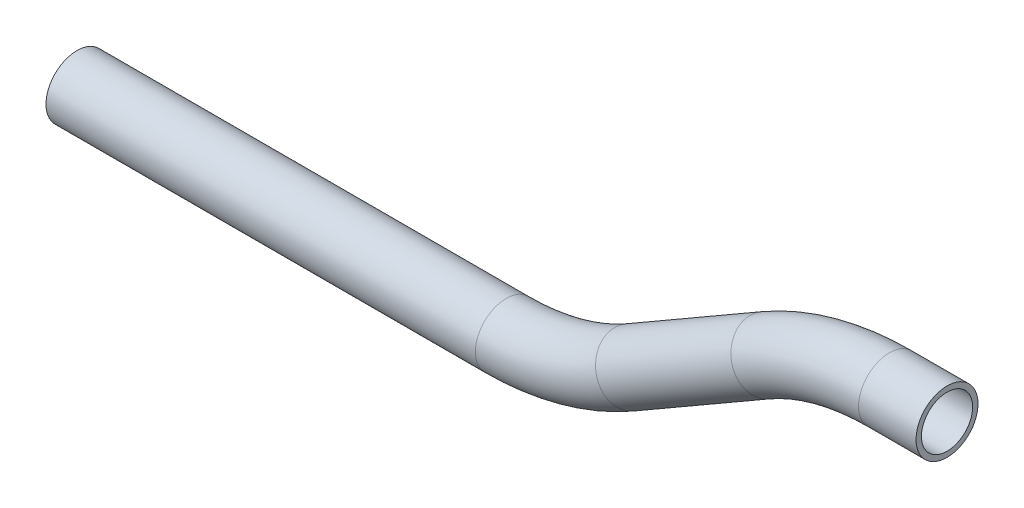
SolidWorks part; units mm, degrees
material "6061 Alloy"
ref_plane "Front Plane" through (0, 0, 0) normal (0, 0, 1) x (1, 0, 0)
ref_plane "Top Plane" through (0, 0, 0) normal (0, 1, 0) x (1, 0, 0)
ref_plane "Right Plane" through (0, 0, 0) normal (1, 0, 0) x (0, 0, -1)
sketch "Sketch4" plane through (0, 0, 0) normal (0, 0, 1) x (1, 0, 0)
  line L0 (27.5339, 15.1508) -> (45.2162, 15.1508)
  line L2 (-10.5661, 4.9419) -> (-52.1912, -19.0903)
  line L3 (-52.1912, -19.0903) -> (7.1162, 15.1508)
  line L4 (45.2162, 15.1508) -> (7.1162, 15.1508)
  line L5 (-90.2912, -29.2992) -> (-222.2735, -29.2992)
  line L6 (-222.2735, -29.2992) -> (-69.8735, -29.2992)
  line L7 (-10.5661, 4.9419) -> (-69.8735, -29.2992)
  arc A0 (27.5339, 15.1508) -> (-10.5661, 4.9419) centre (27.5339, -61.0492) ccw
  arc A1 (-52.1912, -19.0903) -> (-90.2912, -29.2992) centre (-90.2912, 46.9008) cw
  point P9 (7.1162, 15.1508)
  point P14 (-69.8735, -29.2992)
  dimension "D3" = 30
  dimension "D4" = 30
  dimension "D1" = 76.2
  dimension "D2" = 76.2
  dimension "D5" = 88.9
  dimension "D6" = 38.1
  dimension "D7" = 152.4
ref_plane "Plane2" through (45.2162, 15.1508, 0) normal (-1, 0, 0) x (0, 0, 1)
sketch "Sketch5" plane through (45.2162, 15.1508, 0) normal (-1, 0, 0) x (0, 0, 1)
  circle A0 centre (0, 0) radius 9.525
  circle A1 centre (0, 0) radius 7.874
  dimension "D1" = 15.748
  dimension "D2" = 19.05
sweep "Sweep1" add profiles "Sketch5" path "Sketch4"
sketch "Sketch6" plane through (-222.2735, 0, 0) normal (-1, 0, 0) x (0, 0, 1)
  line L0 (-7.874, -29.2992) -> (7.874, -29.2992) construction
sketch "Sketch7" plane through (0, 0, 0) normal (0, 0, 1) x (1, 0, 0)
  line L0 (-222.2735, -29.2992) -> (-136.2487, -29.2992) construction
  line L1 (-222.2735, -19.7742) -> (-222.2735, -38.8242) construction
